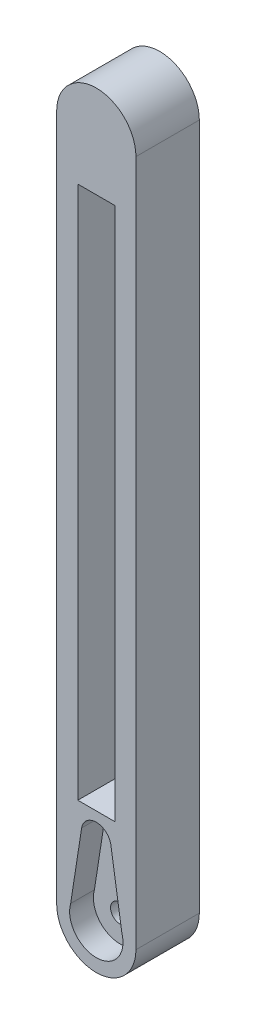
SolidWorks part; units mm, degrees
ref_plane "Front Plane" through (0, 0, 0) normal (0, 0, 1) x (1, 0, 0)
ref_plane "Top Plane" through (0, 0, 0) normal (0, 1, 0) x (1, 0, 0)
ref_plane "Right Plane" through (0, 0, 0) normal (1, 0, 0) x (0, 0, -1)
sketch "Sketch1" plane through (0, 0, 0) normal (0, 0, 1) x (1, 0, 0)
  line L0 (-5.6452, 102.5806) -> (-5.6452, -27.4194)
  line L1 (9.3548, 102.5806) -> (9.3548, -27.4194)
  arc A0 (-5.6452, 102.5806) -> (9.3548, 102.5806) centre (1.8548, 102.5806) cw
  arc A1 (-5.6452, -27.4194) -> (9.3548, -27.4194) centre (1.8548, -27.4194) ccw
  dimension "D1" = 15
  dimension "D2" = 130
extrude "Boss-Extrude1" add sketch "Sketch1" along normal blind 12
sketch "Sketch5" plane through (0, 0, 12) normal (0, 0, 1) x (1, 0, 0)
  line L0 (-5.6452, 102.5806) -> (-5.6452, -27.4194) construction
  line L1 (-1.6452, -19.9194) -> (-5.6452, -19.9194) construction
  line L2 (-1.6452, -19.9194) -> (-1.6452, 92.5806) construction
  line L3 (-1.6452, 92.5806) -> (-5.6452, 92.5806) construction
  line L4 (-5.6452, -19.9194) -> (-5.6452, 92.5806) construction
  line L6 (5.3548, -19.9194) -> (9.3548, -19.9194) construction
  line L7 (5.3548, -19.9194) -> (5.3548, 92.5806) construction
  line L8 (5.3548, 92.5806) -> (9.3548, 92.5806) construction
  line L9 (9.3548, -19.9194) -> (9.3548, 92.5806) construction
  line L10 (-1.6452, 92.5806) -> (5.3548, 92.5806)
  line L11 (-1.6452, 92.5806) -> (-1.6452, -19.9194)
  line L12 (-1.6452, -19.9194) -> (5.3548, -19.9194)
  line L13 (5.3548, 92.5806) -> (5.3548, -19.9194)
  arc A0 (-5.6452, -27.4194) -> (9.3548, -27.4194) centre (1.8548, -27.4194) cw construction
  arc A1 (9.3548, 102.5806) -> (-5.6452, 102.5806) centre (1.8548, 102.5806) ccw construction
  dimension "D1" = 4
  dimension "D2" = 4
  dimension "D3" = 10
extrude "Cut-Extrude3" cut sketch "Sketch5" against normal blind 12
sketch "Sketch6" plane through (-5.6452, 0, 0) normal (-1, 0, 0) x (0, 0, 1)
  line L0 (6, 102.5806) -> (6, 14.8619) construction
  line L1 (12, 102.5806) -> (0, 102.5806) construction
  circle A0 centre (6, 78.769) radius 5.15
  circle A1 centre (6, 53.769) radius 5.15
  circle A2 centre (6, 28.769) radius 5.15
  dimension "D1" = 3
extrude "Cut-Extrude4" cut sketch "Sketch6" against normal blind 2
sketch "Sketch7" plane through (0, 0, 12) normal (0, 0, 1) x (1, 0, 0)
  line L1 (-2.3763, -21.0426) -> (7.0786, -21.0426)
  line L2 (-2.3763, -21.0426) -> (-2.3763, -8.415)
  line L3 (-2.3763, -8.415) -> (7.0786, -8.415)
  line L4 (7.0786, -21.0426) -> (7.0786, -8.415)
extrude "Boss-Extrude2" add sketch "Sketch7" against normal blind 12
sketch "Sketch8" plane through (0, 0, 12) normal (0, 0, 1) x (1, 0, 0)
  line L0 (6.6938, -25.9617) -> (4.6114, -12.5925)
  line L1 (-0.9208, -12.5925) -> (-2.9973, -26.0062)
  line L2 (-5.6452, 102.5806) -> (-5.6452, -27.4194) construction
  circle A3 centre (1.8548, -27.4194) radius 1.8
  arc A4 (-2.9973, -26.0062) -> (6.6938, -25.9617) centre (1.8548, -27.4194) ccw
  arc A5 (4.6114, -12.5925) -> (-0.9208, -12.5925) centre (1.8453, -13.076) ccw
  arc A6 (-5.6452, -27.4194) -> (9.3548, -27.4194) centre (1.8548, -27.4194) ccw construction
  point P14 (2.3803, -22.2211)
  point P17 (1.8548, -34.9194)
  dimension "D1" = 7.5
  dimension "D2" = 7.5
extrude "Cut-Extrude5" cut sketch "Sketch8" against normal blind 4.5
sketch "Sketch9" plane through (0, 0, 12) normal (0, 0, 1) x (1, 0, 0)
  circle A0 centre (1.8548, -27.4194) radius 1.8
extrude "Cut-Extrude6" cut sketch "Sketch9" against normal blind 13.5
sketch "Sketch10" plane through (0, 0, 0) normal (0, 0, -1) x (-1, 0, 0)
  circle A0 centre (-1.8548, -27.4194) radius 2.25
extrude "Cut-Extrude7" cut sketch "Sketch10" against normal blind 2
